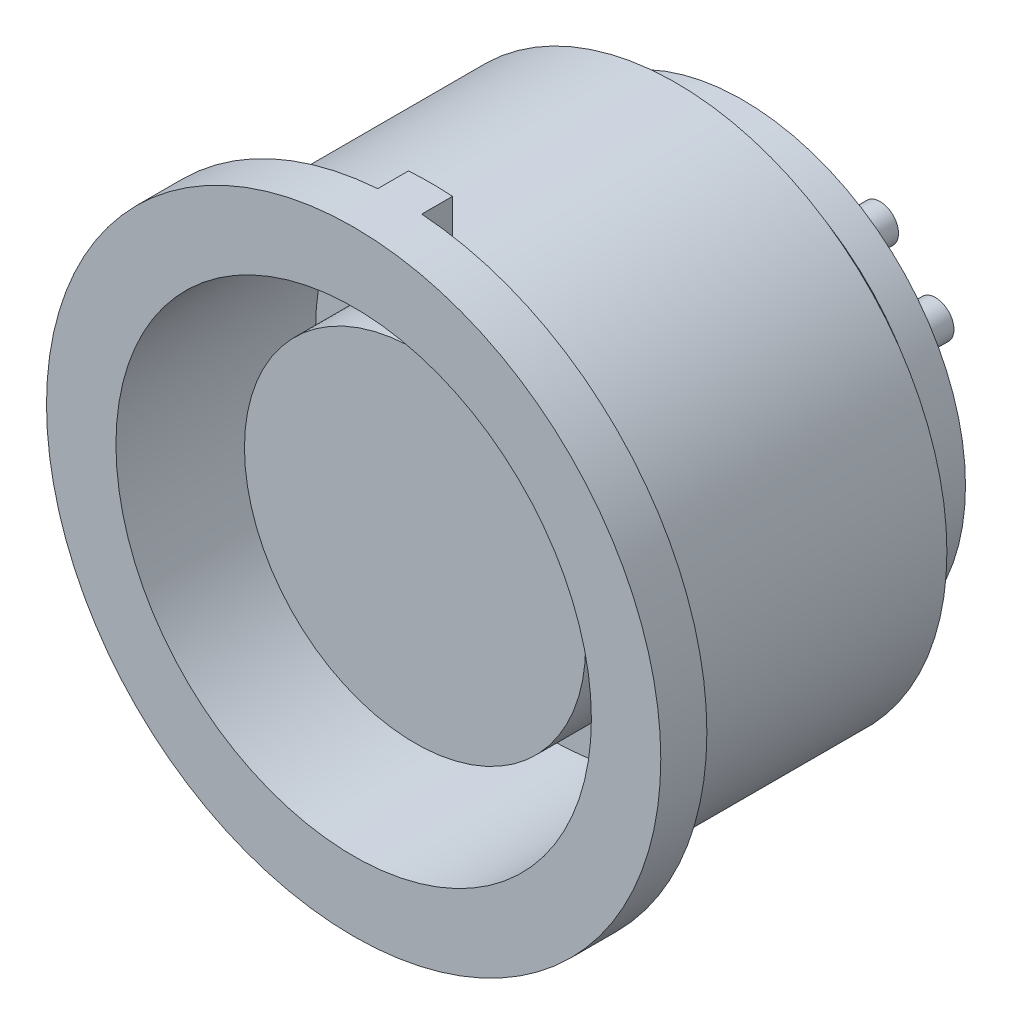
SolidWorks part; units mm, degrees
ref_plane "Front Plane" through (0, 0, 0) normal (0, 0, 1) x (1, 0, 0)
ref_plane "Top Plane" through (0, 0, 0) normal (0, 1, 0) x (1, 0, 0)
ref_plane "Right Plane" through (0, 0, 0) normal (1, 0, 0) x (0, 0, -1)
sketch "Sketch2" plane through (0, 0, 0) normal (1, 0, 0) x (0, 0, -1)
  line L0 (0, 8.815) -> (0, 10)
  line L1 (0, 10) -> (-1.5, 10)
  line L2 (-1.5, 10) -> (-1.5, 7.74)
  line L3 (-1.5, 7.74) -> (5, 7.74)
  line L4 (5, 7.74) -> (5, 5.555)
  line L5 (5, 5.555) -> (0.5, 5.555)
  line L6 (0.5, 5.555) -> (0.5, 0)
  line L7 (0, 8.815) -> (9, 8.815)
  line L8 (9, 8.815) -> (10.1308, 7.25)
  line L9 (10.1308, 7.25) -> (11.17, 7.25)
  line L10 (11.17, 7.25) -> (11.17, 0)
  line L11 (11.17, 0) -> (0.5, 0)
  line L12 (-11.3571, 0) -> (35.3571, 0) construction
  dimension "D1" = 20
  dimension "D2" = 2.26
  dimension "D3" = 17.63
  dimension "D4" = 14.5
  dimension "D5" = 9
  dimension "D6" = 12.67
  dimension "D7" = 1.5
  dimension "D8" = 6.5
  dimension "D9" = 11.11
  dimension "D10" = 2
revolve "Revolve1" add sketch "Sketch2" angle 360 about L12
sketch "Sketch3" plane through (0, 0, -11.17) normal (0, 0, -1) x (-1, 0, 0)
  circle A0 centre (1.714, 3.7737) radius 0.6
  circle A1 centre (1.714, 1.9686) radius 0.6
  circle A2 centre (3.5212, 1.9686) radius 0.6
  dimension "D1" = 1.2
extrude "Boss-Extrude1" add sketch "Sketch3" along normal blind 2.5
pattern_circular "CirPattern1" count 4 over 360 about axis through (0, 0, 0) along (0, 0, 1) of "Boss-Extrude1"
sketch "Sketch5" plane through (0, 0, 0) normal (0, 0, -1) x (-1, 0, 0)
  line L0 (-0.7167, 9.9743) -> (-0.7167, 8.7858)
  line L1 (0.7167, 9.9743) -> (0.7167, 8.7858)
  line L2 (0, 0) -> (0, 10.7712) construction
  circle A0 centre (0, 0) radius 10 construction
  circle A1 centre (0, 0) radius 8.815 construction
  circle A2 centre (0, 0) radius 8.815 construction
  arc A3 (0.7167, 8.7858) -> (-0.7167, 8.7858) centre (0, 0) ccw
  arc A4 (0.7167, 9.9743) -> (-0.7167, 9.9743) centre (0, 0) ccw
extrude "Boss-Extrude2" add sketch "Sketch5" along normal blind 1
